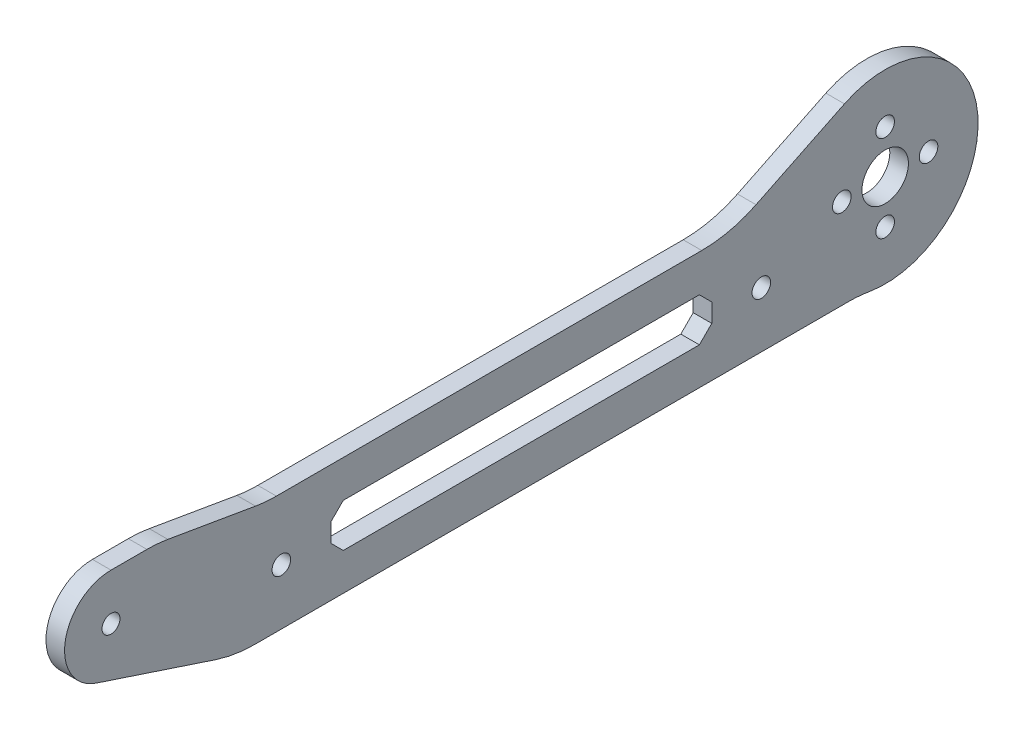
SolidWorks part; units mm, degrees
ref_plane "Front Plane" through (0, 0, 0) normal (0, 0, 1) x (1, 0, 0)
ref_plane "Top Plane" through (0, 0, 0) normal (0, 1, 0) x (1, 0, 0)
ref_plane "Right Plane" through (0, 0, 0) normal (1, 0, 0) x (0, 0, -1)
sketch "Sketch1" plane through (0, 0, 0) normal (1, 0, 0) x (0, 0, -1)
  line L0 (0, 0) -> (-125, 0) construction
  line L1 (-105, -14.5) -> (-3.8406, -14.5)
  line L2 (-105, -14.5) -> (-127.351, -7.122)
  line L3 (-125, 7.5) -> (-117.5, 7.5)
  line L4 (-117.5, 7.5) -> (-100, 4.5)
  line L5 (-100, 4.5) -> (-25, 4.5)
  line L6 (-25, 4.5) -> (-6.573, 13.4831)
  line L7 (-89.5, -3.5) -> (-87.5, -1.5)
  line L8 (-60, -5.5) -> (-97.5, -5.5) construction
  line L9 (-60, -5.5) -> (-20, -5.5) construction
  line L10 (-87.5, -1.5) -> (-30, -1.5)
  line L11 (-89.5, -3.5) -> (-89.5, -6.5)
  line L12 (-87.5, -8.5) -> (-30, -8.5)
  line L13 (-28, -3.5) -> (-28, -6.5)
  line L14 (-89.5, -6.5) -> (-87.5, -8.5)
  line L15 (-30, -1.5) -> (-28, -3.5)
  line L16 (-30, -8.5) -> (-28, -6.5)
  circle A0 centre (0, 7) radius 1.5
  circle A1 centre (0, -7) radius 1.5
  circle A2 centre (7, 0) radius 1.5
  circle A3 centre (-7, 0) radius 1.5
  circle A15 centre (-125, 0) radius 1.45
  circle A16 centre (-125, 0) radius 7.5
  circle A17 centre (0, 0) radius 15
  circle A18 centre (0, 0) radius 3.75
  circle A22 centre (-97.5, -5.5) radius 1.5
  circle A23 centre (-20, -5.5) radius 1.5
  point P1 (-3.75, 0)
  point P13 (-89.5, -1.5)
  point P14 (-28, -8.5)
  point P15 (-89.5, -8.5)
  point P16 (-28, -1.5)
  point P35 (0, 0)
  dimension "D3" = 125
  dimension "D6" = 7
  dimension "D10" = 7.5
  dimension "D5" = 2.9
  dimension "D8" = 30
  dimension "D9" = 15
  dimension "D12" = 25
  dimension "D13" = 25
  dimension "D19" = 6
  dimension "D14" = 7.5
  dimension "D16" = 20
  dimension "D17" = 3
  dimension "D18" = 27.5
  dimension "D20" = 6
  dimension "D21" = 20
  dimension "D22" = 77.5
  dimension "D24" = 65
  dimension "D26" = 3
  dimension "D27" = 3
  dimension "D28" = 3
  dimension "D29" = 3
  dimension "D4" = 7
  dimension "D7" = 7
  dimension "D11" = 4.5
  dimension "D15" = 14.5
  dimension "D23" = 5.5
  dimension "D25" = 7
  dimension "D30" = 8
  dimension "D31" = 8
extrude "Boss-Extrude1" add sketch "Sketch1" along normal mid plane 3
fillet "Fillet1" radius 20 5 edges at (0, -14.5, 3.8406) (0, 7.5, 117.5) (0, 4.5, 100) (0, 4.5, 25) (0, -14.5, 105)
